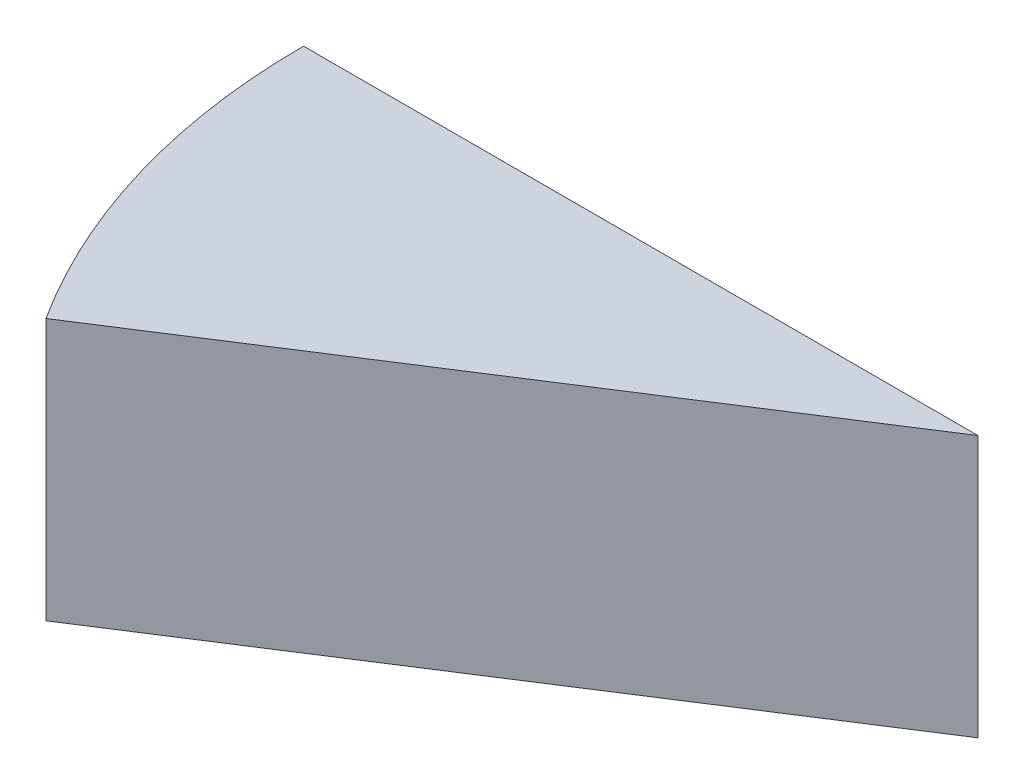
SolidWorks part; units mm, degrees
ref_plane "Front Plane" through (0, 0, 0) normal (0, 0, 1) x (1, 0, 0)
ref_plane "Top Plane" through (0, 0, 0) normal (0, 1, 0) x (1, 0, 0)
ref_plane "Right Plane" through (0, 0, 0) normal (1, 0, 0) x (0, 0, -1)
sketch "Sketch1" plane through (0, 0, 0) normal (0, 1, 0) x (1, 0, 0)
  line L0 (-77.2829, 0) -> (0, 0)
  line L1 (0, 0) -> (-65.0145, -41.7823)
  arc A0 (-77.2829, 0) -> (-65.0145, -41.7823) centre (0, 0) ccw
  dimension "D1" = 32.727
  dimension "D2" = 77.2829
extrude "Boss-Extrude1" add sketch "Sketch1" along normal blind 30
